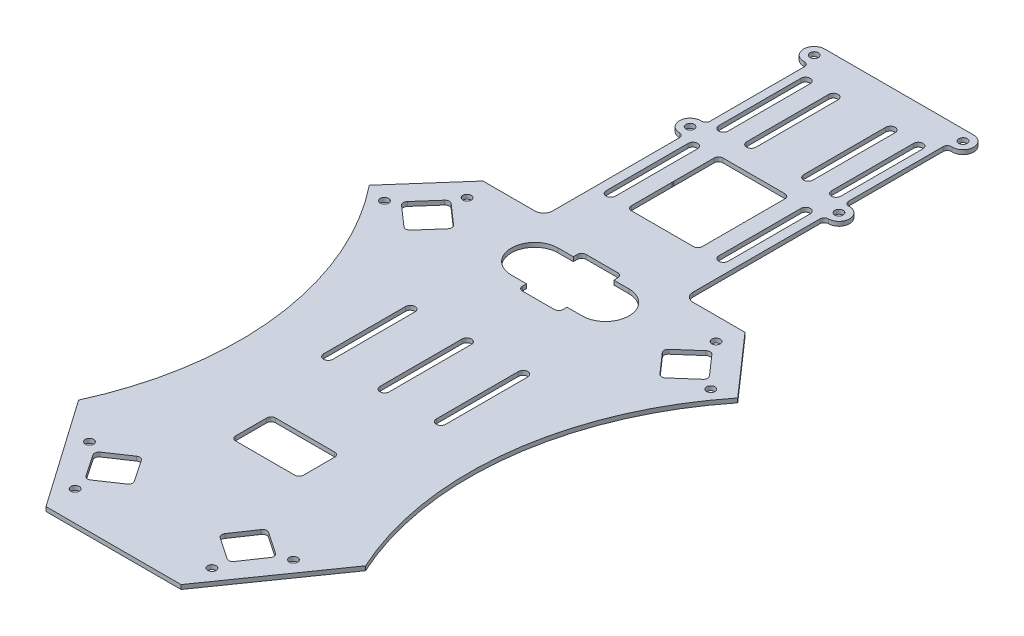
SolidWorks part; units mm, degrees
ref_plane "Front Plane" through (0, 0, 0) normal (0, 0, 1) x (1, 0, 0)
ref_plane "Top Plane" through (0, 0, 0) normal (0, 1, 0) x (1, 0, 0)
ref_plane "Right Plane" through (0, 0, 0) normal (1, 0, 0) x (0, 0, -1)
sketch "Sketch1" plane through (0, 0, 0) normal (0, 1, 0) x (1, 0, 0)
  line L0 (0, -163.8605) -> (0, 187.1526) construction
  line L1 (24.225, -100.314) -> (-24.225, -100.314)
  line L2 (-47, 79.196) -> (-66.075, 57.4987)
  line L3 (-51.475, -61.3813) -> (-24.225, -100.314)
  line L4 (-47, 79.196) -> (-28.38, 79.196)
  line L5 (-25.2, 82.376) -> (-25.2, 127.896)
  line L6 (26.7, 181.496) -> (-26.7, 181.496)
  line L7 (-24.85, 172.4076) -> (-24.85, 138.4845)
  line L8 (-20.22, 168.1277) -> (-20.22, 138.6677) construction
  line L9 (-18.54, 168.1277) -> (-18.54, 138.6677)
  line L10 (-21.9, 168.1277) -> (-21.9, 138.6677)
  line L11 (-10.22, 168.1277) -> (-10.22, 138.6677) construction
  line L12 (-8.54, 168.1277) -> (-8.54, 138.6677)
  line L13 (-11.9, 168.1277) -> (-11.9, 138.6677)
  line L14 (-20.22, 127.716) -> (-20.22, 98.256) construction
  line L15 (-18.54, 127.716) -> (-18.54, 98.256)
  line L16 (-21.9, 127.716) -> (-21.9, 98.256)
  line L17 (-20.22, 26.376) -> (-20.22, -3.084) construction
  line L18 (-18.54, 26.376) -> (-18.54, -3.084)
  line L19 (-21.9, 26.376) -> (-21.9, -3.084)
  line L20 (0, 26.376) -> (0, -3.084) construction
  line L21 (1.68, 26.376) -> (1.68, -3.084)
  line L22 (-1.68, 26.376) -> (-1.68, -3.084)
  line L23 (-54.1827, 59.2578) -> (-47.9366, 66.3626)
  line L24 (11.13, 129.396) -> (-11.13, 129.396)
  line L25 (12.7, 127.826) -> (12.7, 113.506)
  line L26 (11.13, 111.936) -> (-11.13, 111.936)
  line L27 (-12.7, 127.826) -> (-12.7, 113.506)
  line L28 (12.7, 129.396) -> (-12.7, 111.936) construction
  line L29 (12.7, 111.936) -> (-12.7, 129.396) construction
  line L30 (11.13, 114.036) -> (-11.13, 114.036)
  line L31 (12.7, 112.466) -> (12.7, 98.146)
  line L32 (11.13, 96.576) -> (-11.13, 96.576)
  line L33 (-12.7, 112.466) -> (-12.7, 98.146)
  line L34 (12.7, 114.036) -> (-12.7, 96.576) construction
  line L35 (12.7, 96.576) -> (-12.7, 114.036) construction
  line L36 (-54.0402, 57.0421) -> (-46.9354, 50.796)
  line L37 (-45.7209, 66.5051) -> (-38.6161, 60.2591)
  line L38 (-44.7197, 50.9385) -> (-38.4736, 58.0433)
  line L39 (-31.8561, -75.8408) -> (-26.6116, -83.5936)
  line L40 (-12.7, 71.876) -> (-7.265, 71.876)
  line L41 (-12.7, 55.076) -> (-7.265, 55.076)
  line L42 (7.265, 71.876) -> (12.7, 71.876)
  line L43 (5.695, 74.876) -> (-5.695, 74.876)
  line L44 (7.265, 73.306) -> (7.265, 71.876)
  line L45 (5.695, 52.076) -> (-5.695, 52.076)
  line L46 (-7.265, 73.306) -> (-7.265, 71.876)
  line L47 (7.265, 74.876) -> (6.9033, 74.3085) construction
  line L48 (7.265, 52.076) -> (6.9033, 52.6436) construction
  line L49 (7.265, 55.076) -> (7.265, 53.646)
  line L50 (-7.265, 55.076) -> (-7.265, 53.646)
  line L51 (-6.9033, 52.6436) -> (-7.265, 52.076) construction
  line L52 (7.265, 55.076) -> (12.7, 55.076)
  line L53 (-6.9033, 74.3085) -> (-7.265, 74.876) construction
  line L54 (-31.4354, -73.6607) -> (-23.6827, -68.4162)
  line L55 (-24.4315, -84.0143) -> (-16.6788, -78.7698)
  line L56 (-21.5026, -68.837) -> (-16.2581, -76.5897)
  line L57 (24.4315, -84.0143) -> (16.6788, -78.7698)
  line L58 (10.615, -31.604) -> (-10.615, -31.604)
  line L59 (12.185, -33.174) -> (12.185, -44.354)
  line L60 (10.615, -45.924) -> (-10.615, -45.924)
  line L61 (-12.185, -33.174) -> (-12.185, -44.354)
  line L62 (12.185, -31.604) -> (-12.185, -45.924) construction
  line L63 (12.185, -45.924) -> (-12.185, -31.604) construction
  line L64 (21.5026, -68.837) -> (16.2581, -76.5897)
  line L65 (31.4354, -73.6607) -> (23.6827, -68.4162)
  line L66 (31.8561, -75.8408) -> (26.6116, -83.5936)
  line L67 (51.475, -61.3813) -> (24.225, -100.314)
  line L68 (20.22, 26.376) -> (20.22, -3.084) construction
  line L69 (18.54, 26.376) -> (18.54, -3.084)
  line L70 (21.9, 26.376) -> (21.9, -3.084)
  line L71 (54.0402, 57.0421) -> (46.9354, 50.796)
  line L72 (44.7197, 50.9385) -> (38.4736, 58.0433)
  line L73 (45.7209, 66.5051) -> (38.6161, 60.2591)
  line L74 (54.1827, 59.2578) -> (47.9366, 66.3626)
  line L75 (47, 79.196) -> (66.075, 57.4987)
  line L76 (47, 79.196) -> (28.38, 79.196)
  line L77 (20.22, 127.716) -> (20.22, 98.256) construction
  line L78 (18.54, 127.716) -> (18.54, 98.256)
  line L79 (21.9, 127.716) -> (21.9, 98.256)
  line L80 (10.22, 168.1277) -> (10.22, 138.6677) construction
  line L81 (8.54, 168.1277) -> (8.54, 138.6677)
  line L82 (11.9, 168.1277) -> (11.9, 138.6677)
  line L83 (20.22, 168.1277) -> (20.22, 138.6677) construction
  line L84 (18.54, 168.1277) -> (18.54, 138.6677)
  line L85 (21.9, 168.1277) -> (21.9, 138.6677)
  line L86 (25.2, 82.376) -> (25.2, 127.896)
  line L87 (24.85, 172.4076) -> (24.85, 138.4845)
  arc A0 (-51.475, -61.3813) -> (-66.075, 57.4987) centre (-155.1713, -13.7801) ccw
  arc A1 (-26.7, 181.496) -> (-26.4491, 173.9043) centre (-26.7, 177.696) ccw
  arc A2 (-26.4491, 136.9877) -> (-26.7, 129.396) centre (-26.7, 133.196) ccw
  arc A3 (-25.2, 127.896) -> (-26.7, 129.396) centre (-26.7, 127.896) ccw
  arc A4 (-24.85, 138.4845) -> (-26.4491, 136.9877) centre (-26.35, 138.4845) cw
  arc A5 (-24.85, 172.4076) -> (-26.4491, 173.9043) centre (-26.35, 172.4076) ccw
  arc A6 (-25.2, 82.376) -> (-28.38, 79.196) centre (-28.38, 82.376) cw
  arc A7 (-18.54, 168.1277) -> (-21.9, 168.1277) centre (-20.22, 168.1277) ccw
  arc A8 (-21.9, 138.6677) -> (-18.54, 138.6677) centre (-20.22, 138.6677) ccw
  arc A9 (-8.54, 168.1277) -> (-11.9, 168.1277) centre (-10.22, 168.1277) ccw
  arc A10 (-11.9, 138.6677) -> (-8.54, 138.6677) centre (-10.22, 138.6677) ccw
  arc A11 (-18.54, 127.716) -> (-21.9, 127.716) centre (-20.22, 127.716) ccw
  arc A12 (-21.9, 98.256) -> (-18.54, 98.256) centre (-20.22, 98.256) ccw
  arc A13 (-18.54, 26.376) -> (-21.9, 26.376) centre (-20.22, 26.376) ccw
  arc A14 (-21.9, -3.084) -> (-18.54, -3.084) centre (-20.22, -3.084) ccw
  arc A15 (1.68, 26.376) -> (-1.68, 26.376) centre (0, 26.376) ccw
  arc A16 (-1.68, -3.084) -> (1.68, -3.084) centre (0, -3.084) ccw
  arc A17 (11.13, 96.576) -> (12.7, 98.146) centre (11.13, 98.146) ccw
  arc A18 (12.7, 112.466) -> (11.13, 114.036) centre (11.13, 112.466) ccw
  arc A19 (-12.7, 112.466) -> (-11.13, 114.036) centre (-11.13, 112.466) cw
  arc A20 (-11.13, 96.576) -> (-12.7, 98.146) centre (-11.13, 98.146) cw
  arc A21 (12.7, 113.506) -> (11.13, 111.936) centre (11.13, 113.506) cw
  arc A22 (-11.13, 111.936) -> (-12.7, 113.506) centre (-11.13, 113.506) cw
  arc A23 (-11.13, 129.396) -> (-12.7, 127.826) centre (-11.13, 127.826) ccw
  arc A24 (12.7, 127.826) -> (11.13, 129.396) centre (11.13, 127.826) ccw
  arc A25 (-46.9354, 50.796) -> (-44.7197, 50.9385) centre (-45.8988, 51.9751) ccw
  arc A26 (-54.0402, 57.0421) -> (-54.1827, 59.2578) centre (-53.0036, 58.2212) cw
  arc A27 (-38.4736, 58.0433) -> (-38.6161, 60.2591) centre (-39.6527, 59.0799) ccw
  arc A28 (-45.7209, 66.5051) -> (-47.9366, 66.3626) centre (-46.7575, 65.326) ccw
  arc A29 (-12.7, 71.876) -> (-12.7, 55.076) centre (-12.7, 63.476) ccw
  arc A30 (12.7, 55.076) -> (12.7, 71.876) centre (12.7, 63.476) ccw
  arc A31 (7.265, 53.646) -> (5.695, 52.076) centre (5.695, 53.646) cw
  arc A32 (7.265, 73.306) -> (5.695, 74.876) centre (5.695, 73.306) ccw
  arc A33 (-5.695, 74.876) -> (-7.265, 73.306) centre (-5.695, 73.306) ccw
  arc A34 (-7.265, 53.646) -> (-5.695, 52.076) centre (-5.695, 53.646) ccw
  arc A35 (-26.6116, -83.5936) -> (-24.4315, -84.0143) centre (-25.3112, -82.7139) ccw
  arc A36 (-16.6788, -78.7698) -> (-16.2581, -76.5897) centre (-17.5585, -77.4694) ccw
  arc A37 (-21.5026, -68.837) -> (-23.6827, -68.4162) centre (-22.803, -69.7166) ccw
  arc A38 (-31.8561, -75.8408) -> (-31.4354, -73.6607) centre (-30.5557, -74.9611) cw
  arc A39 (-12.185, -33.174) -> (-10.615, -31.604) centre (-10.615, -33.174) cw
  arc A40 (10.615, -31.604) -> (12.185, -33.174) centre (10.615, -33.174) cw
  arc A41 (12.185, -44.354) -> (10.615, -45.924) centre (10.615, -44.354) cw
  arc A42 (-10.615, -45.924) -> (-12.185, -44.354) centre (-10.615, -44.354) cw
  arc A43 (21.5026, -68.837) -> (23.6827, -68.4162) centre (22.803, -69.7166) cw
  arc A44 (46.9354, 50.796) -> (44.7197, 50.9385) centre (45.8988, 51.9751) cw
  arc A45 (45.7209, 66.5051) -> (47.9366, 66.3626) centre (46.7575, 65.326) cw
  arc A46 (54.0402, 57.0421) -> (54.1827, 59.2578) centre (53.0036, 58.2212) ccw
  arc A47 (38.4736, 58.0433) -> (38.6161, 60.2591) centre (39.6527, 59.0799) cw
  arc A48 (16.6788, -78.7698) -> (16.2581, -76.5897) centre (17.5585, -77.4694) cw
  arc A49 (26.6116, -83.5936) -> (24.4315, -84.0143) centre (25.3112, -82.7139) cw
  arc A50 (31.8561, -75.8408) -> (31.4354, -73.6607) centre (30.5557, -74.9611) ccw
  arc A51 (18.54, 26.376) -> (21.9, 26.376) centre (20.22, 26.376) cw
  arc A52 (21.9, -3.084) -> (18.54, -3.084) centre (20.22, -3.084) cw
  arc A53 (51.475, -61.3813) -> (66.075, 57.4987) centre (155.1713, -13.7801) cw
  arc A54 (25.2, 82.376) -> (28.38, 79.196) centre (28.38, 82.376) ccw
  arc A55 (18.54, 127.716) -> (21.9, 127.716) centre (20.22, 127.716) cw
  arc A56 (21.9, 98.256) -> (18.54, 98.256) centre (20.22, 98.256) cw
  arc A57 (8.54, 168.1277) -> (11.9, 168.1277) centre (10.22, 168.1277) cw
  arc A58 (11.9, 138.6677) -> (8.54, 138.6677) centre (10.22, 138.6677) cw
  arc A59 (18.54, 168.1277) -> (21.9, 168.1277) centre (20.22, 168.1277) cw
  arc A60 (21.9, 138.6677) -> (18.54, 138.6677) centre (20.22, 138.6677) cw
  arc A61 (25.2, 127.896) -> (26.7, 129.396) centre (26.7, 127.896) cw
  arc A62 (26.4491, 136.9877) -> (26.7, 129.396) centre (26.7, 133.196) cw
  arc A63 (24.85, 138.4845) -> (26.4491, 136.9877) centre (26.35, 138.4845) ccw
  arc A64 (24.85, 172.4076) -> (26.4491, 173.9043) centre (26.35, 172.4076) cw
  arc A65 (26.7, 181.496) -> (26.4491, 173.9043) centre (26.7, 177.696) cw
  point P23 (-24.85, 174.3768)
  point P26 (-25.2, 79.196)
  point P29 (-20.22, 153.3977)
  point P34 (-10.22, 153.3977)
  point P41 (-20.22, 136.9877)
  point P42 (0, 105.306)
  point P45 (-20.22, 112.986)
  point P50 (-20.22, 96.576)
  point P53 (-20.22, 129.396)
  point P58 (-20.22, 11.646)
  point P68 (0, 11.646)
  point P76 (-51.0597, 62.8102)
  point P77 (0, 120.666)
  point P118 (-46.9, 67.5418)
  point P121 (0, 63.476)
  point P126 (0, 63.476)
  point P149 (-29.2339, -79.7172)
  point P154 (-37.85, -80.8477)
  point P157 (-25.7319, -84.894)
  point P166 (0, -38.764)
  point P202 (0, -100.314)
  point P205 (20.22, 11.646)
  point P218 (20.22, 112.986)
  point P225 (10.22, 153.3977)
  point P232 (20.22, 153.3977)
  point P249 (0, 181.496)
  dimension "D1" = 48.45
  dimension "D4" = 114.1
  dimension "D8" = 7.6
  dimension "D9" = 7.6
  dimension "D11" = 49.7
  dimension "D16" = 1.5
  dimension "D17" = 3.18
  dimension "D18" = 1.68
  dimension "D25" = 1.57
  dimension "D29" = 1.57
  dimension "D30" = 8.4
  dimension "D34" = 1.57
  dimension "D35" = 1.57
  dimension "D40" = 1.57
  dimension "D45" = 1.57
  dimension "D2" = 27.25
  dimension "D3" = 14.6
  dimension "D5" = 118.88
  dimension "D6" = 28.89
  dimension "D7" = 21.8
  dimension "D10" = 26.7
  dimension "D12" = 44.5
  dimension "D13" = 6.31
  dimension "D14" = 102.3
  dimension "D15" = 281.81
  dimension "D19" = 29.46
  dimension "D20" = 10
  dimension "D21" = 20.22
  dimension "D22" = 155.12
  dimension "D23" = 25.4
  dimension "D24" = 12.5
  dimension "D27" = 7.77
  dimension "D28" = 21.7
  dimension "D31" = 7.32
  dimension "D32" = 14.53
  dimension "D33" = 22.8
  dimension "D36" = 12.5
  dimension "D37" = 12.5
  dimension "D38" = 7.77
  dimension "D39" = 15.42
  dimension "D42" = 24.37
  dimension "D43" = 14.32
  dimension "D44" = 213.1
  dimension "D46" = 14.32
extrude "Boss-Extrude1" add sketch "Sketch1" along normal blind 1.53 contours A65 L6 A1 A5 L7 A4 A2 A3 L5 A6 L4 L2 A0 L3 L1 L67 A53 L75 L76 A54 L86 A61 A62 A63 L87 A64 A50 L66 A49 L57 A48 L64 A43 L65 A34 L50 L41 A29 L40 L46 A33 L43 A32 L44 L42 A30 L52 L49 A31
sketch "Sketch2" plane through (0, 1.53, 0) normal (0, 1, 0) x (1, 0, 0)
  line L1 (-51.0597, 62.8102) -> (-54.8635, 66.1543) construction
  line L2 (-54.1827, 59.2578) -> (-47.9366, 66.3626) construction
  line L3 (-39.8204, 47.6034) -> (-34.5383, 53.6116) construction
  line L4 (-41.5966, 54.4909) -> (-39.1657, 52.3538) construction
  line L5 (-44.7197, 50.9385) -> (-38.4736, 58.0433) construction
  line L6 (-25.005, 31.646) -> (-25.005, -8.354) construction
  line L7 (-21.9, 26.376) -> (-21.9, -3.084) construction
  line L8 (-12.185, -33.174) -> (-12.185, -44.354) construction
  line L9 (-21.9, 11.646) -> (-28.11, 11.646) construction
  line L10 (0, -116.2483) -> (0, 110.631) construction
  line L12 (-29.2339, -79.7172) -> (-28.8942, -79.4874) construction
  line L13 (-31.8561, -75.8408) -> (-26.6116, -83.5936) construction
  circle A0 centre (-26.7, 177.696) radius 1.5
  circle A1 centre (26.7, 177.696) radius 1.5
  circle A2 centre (-26.7, 133.196) radius 1.5
  circle A3 centre (26.7, 133.196) radius 1.5
  arc A4 (-26.7, 181.496) -> (-26.4491, 173.9043) centre (-26.7, 177.696) ccw construction
  arc A5 (26.4491, 173.9043) -> (26.7, 181.496) centre (26.7, 177.696) ccw construction
  arc A6 (-26.4491, 136.9877) -> (-26.7, 129.396) centre (-26.7, 133.196) ccw construction
  arc A7 (26.7, 129.396) -> (26.4491, 136.9877) centre (26.7, 133.196) ccw construction
  circle A10 centre (-58.5244, 55.3921) radius 1.5
  circle A11 centre (-44.6589, 71.1638) radius 1.5
  arc A12 (-45.7209, 66.5051) -> (-47.9366, 66.3626) centre (-46.7575, 65.326) ccw construction
  circle A17 centre (-36.5725, -72.3745) radius 1.5
  circle A18 centre (-24.5307, -89.579) radius 1.5
  circle A20 centre (36.6774, -72.4467) radius 1.5
  circle A21 centre (24.6356, -89.6512) radius 1.5
  circle A28 centre (58.5244, 55.3921) radius 1.5
  circle A29 centre (44.6589, 71.1638) radius 1.5
  point P10 (0, 0)
  point P28 (0, 0)
  point P32 (-46.8583, 66.8928)
  point P38 (-51.0597, 62.8102)
  point P43 (-37.1793, 50.6075)
  point P44 (-43.9339, 67.7303)
  point P45 (0, 0)
  point P47 (0, 0)
  point P49 (34.1468, -72.0886)
  point P50 (0, 0)
  point P52 (-34.5383, 53.6116)
  point P53 (34.1468, -72.0886)
  point P54 (36.6774, -72.4467)
  point P62 (-25.005, 11.646)
  point P69 (0, 0)
  point P70 (24.2077, -86.7884)
  point P71 (24.6356, -89.6512)
  point P72 (0, 0)
  point P73 (-29.064, -79.6023)
  point P74 (0, 0)
  point P75 (0, 0)
  point P76 (-24.5307, -89.579)
  point P77 (0, 0)
  point P78 (-36.5725, -72.3745)
  point P79 (0, 0)
  point P105 (-43.9, 70.5167)
  point P106 (-44.6589, 71.1638)
  point P108 (0, 0)
  point P109 (-44.6589, 71.1638)
  point P111 (0, 0)
  point P112 (-58.5244, 55.3921)
  point P114 (0, 0)
  dimension "D1" = 3
  dimension "D2" = 3
  dimension "D3" = 12.32
  dimension "D4" = 8
  dimension "D7" = 12.82
  dimension "D8" = 40
extrude "Cut-Extrude1" cut sketch "Sketch2" against normal blind 1.53
